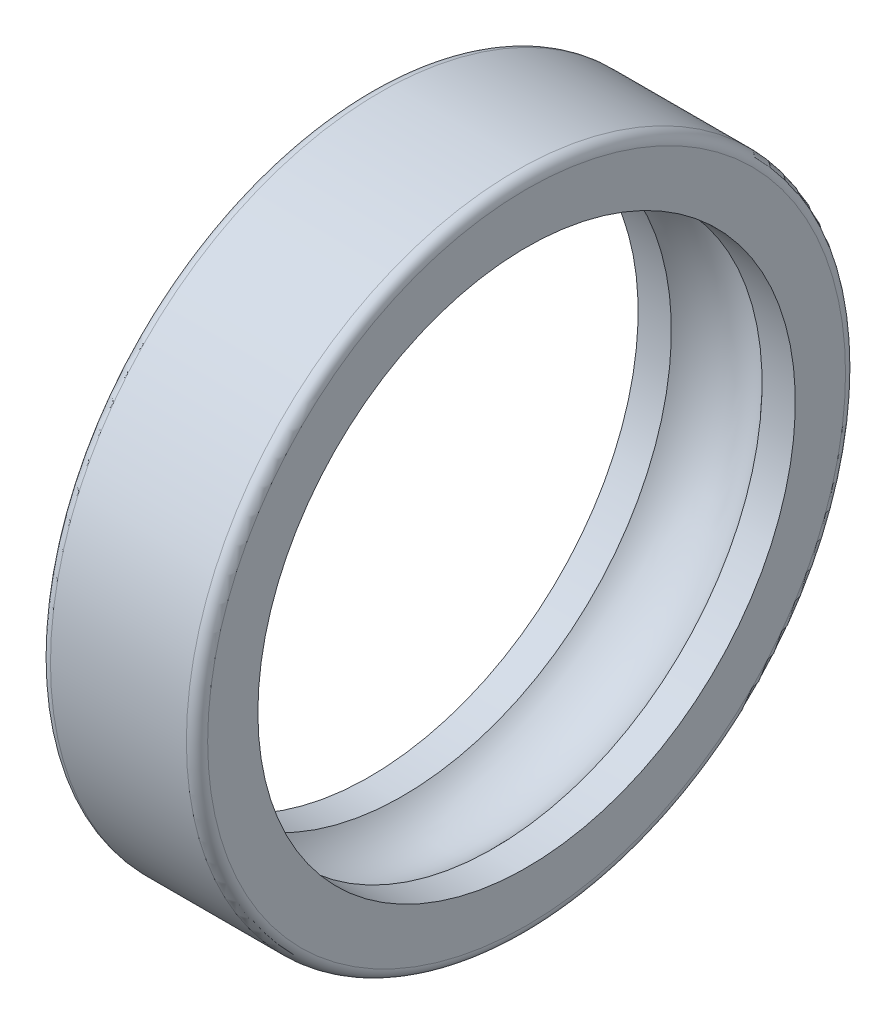
SolidWorks part; units mm, degrees
ref_plane "Front Plane" through (0, 0, 0) normal (0, 0, 1) x (1, 0, 0)
ref_plane "Top Plane" through (0, 0, 0) normal (0, 1, 0) x (1, 0, 0)
ref_plane "Right Plane" through (0, 0, 0) normal (1, 0, 0) x (0, 0, -1)
sketch "Sketch1" plane through (0, 0, 0) normal (0, 0, 1) x (1, 0, 0)
  line L0 (-19.179, 0) -> (29.8285, 0) construction
  line L1 (0, 53) -> (0, 0) construction
  line L2 (-15.5, 65) -> (15.5, 65)
  line L3 (-15.5, 65) -> (-15.5, 53)
  line L4 (-15.5, 53) -> (-8.9443, 53)
  line L5 (15.5, 65) -> (15.5, 53)
  line L6 (-15.5, 65) -> (15.5, 53) construction
  line L7 (-15.5, 53) -> (15.5, 65) construction
  line L8 (8.9443, 53) -> (15.5, 53)
  arc A0 (8.9443, 53) -> (-8.9443, 53) centre (0, 45) ccw
  point P3 (0, 59)
  dimension "D1" = 31
  dimension "D2" = 53
  dimension "D3" = 65
  dimension "D4" = 8
  dimension "D5" = 12
revolve "Revolve1" add sketch "Sketch1" angle 360 about L0
fillet "Fillet1" radius 2.1 2 edges at (15.5, 0, 65) (-15.5, 0, 65)
